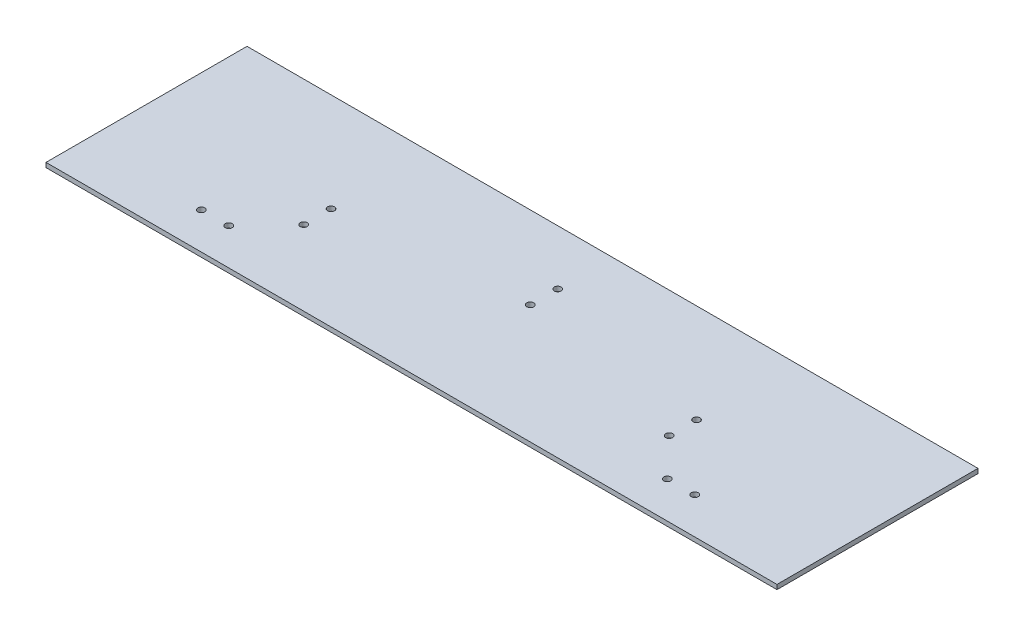
SolidWorks part; units mm, degrees
material "Lexan"
ref_plane "Front Plane" through (0, 0, 0) normal (0, 0, 1) x (1, 0, 0)
ref_plane "Top Plane" through (0, 0, 0) normal (0, 1, 0) x (1, 0, 0)
ref_plane "Right Plane" through (0, 0, 0) normal (1, 0, 0) x (0, 0, -1)
sketch "Sketch1" plane through (0, 0, 0) normal (0, 1, 0) x (1, 0, 0)
  line L1 (0, 0) -> (508, 0)
  line L2 (0, 0) -> (0, -139.7)
  line L3 (0, -139.7) -> (508, -139.7)
  line L4 (508, 0) -> (508, -139.7)
  dimension "D1" = 508
  dimension "D2" = 139.7
extrude "Boss-Extrude1" add sketch "Sketch1" along normal blind 3.175
sketch "Sketch2" plane through (0, 3.175, 0) normal (0, 1, 0) x (1, 0, 0)
  line L0 (0, 0) -> (0, -139.7) construction
  line L1 (0, -139.7) -> (508, -139.7) construction
  line L2 (508, 0) -> (0, 0) construction
  line L3 (508, -139.7) -> (508, 0) construction
  circle A0 centre (82.55, -114.3) radius 2.413
  circle A1 centre (101.6, -114.3) radius 2.413
  circle A2 centre (127, -87.63) radius 2.413
  circle A3 centre (127, -68.58) radius 2.413
  circle A4 centre (254, -38.1) radius 2.413
  circle A5 centre (254, -57.15) radius 2.413
  circle A6 centre (425.45, -114.3) radius 2.413
  circle A7 centre (406.4, -114.3) radius 2.413
  circle A8 centre (381, -87.63) radius 2.413
  circle A9 centre (381, -68.58) radius 2.413
  dimension "D3" = 4.826
  dimension "D4" = 4.826
  dimension "D9" = 4.826
  dimension "D10" = 4.826
  dimension "D13" = 4.826
  dimension "D14" = 4.826
  dimension "D16" = 4.826
  dimension "D17" = 4.826
  dimension "D22" = 4.826
  dimension "D23" = 19.05
  dimension "D24" = 4.826
  dimension "D1" = 82.55
  dimension "D2" = 25.4
  dimension "D5" = 19.05
  dimension "D6" = 52.07
  dimension "D7" = 25.4
  dimension "D8" = 19.05
  dimension "D11" = 38.1
  dimension "D12" = 127
  dimension "D15" = 19.05
  dimension "D18" = 82.55
  dimension "D19" = 19.05
  dimension "D20" = 52.07
  dimension "D21" = 25.4
  dimension "D25" = 25.4
  dimension "D26" = 71.12
  dimension "D27" = 25.4
  dimension "D28" = 25.4
  dimension "D29" = 127
extrude "Cut-Extrude1" cut sketch "Sketch2" against normal up to surface (3.175 mm away) up to face at (254, 0, 69.85)
